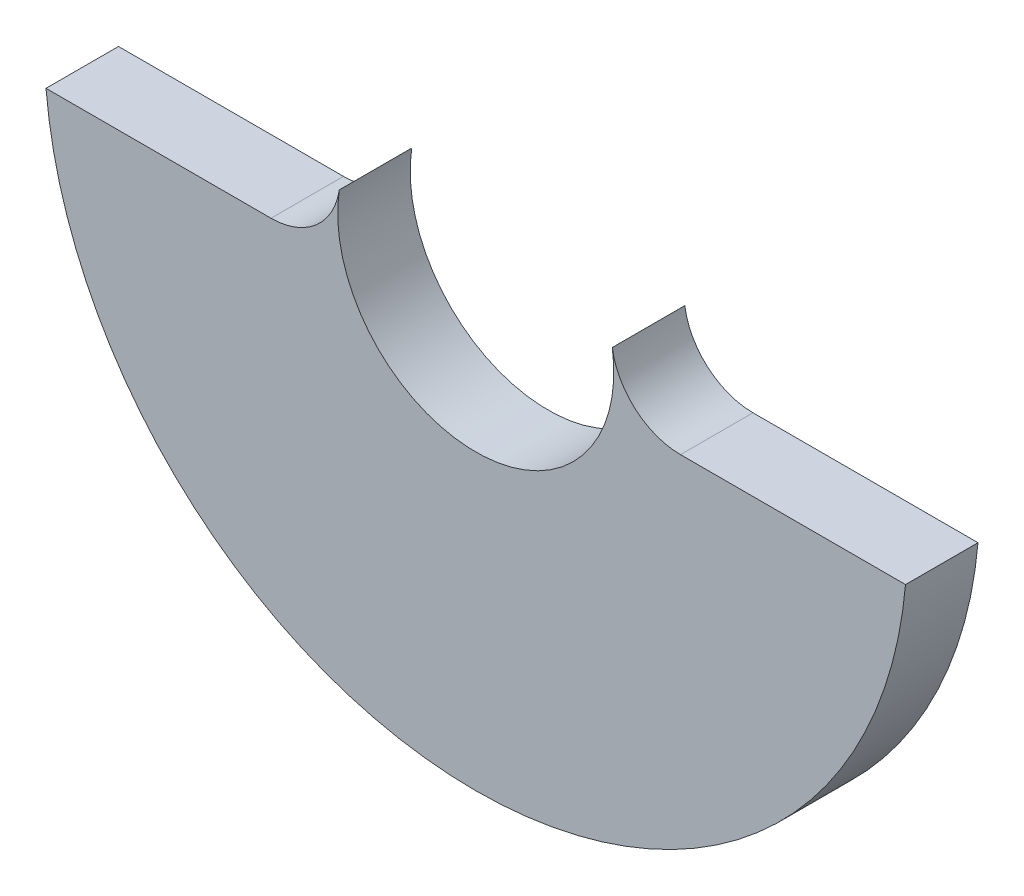
SolidWorks part; units mm, degrees
ref_plane "Front" through (0, 0, 0) normal (0, 0, 1) x (1, 0, 0)
ref_plane "Top" through (0, 0, 0) normal (0, 1, 0) x (1, 0, 0)
ref_plane "Right" through (0, 0, 0) normal (1, 0, 0) x (0, 0, -1)
sketch "Sketch1" plane through (0, 0, 0) normal (0, 0, 1) x (1, 0, 0)
  circle A0 centre (0, 0) radius 25
  circle A1 centre (0, 0) radius 8
  dimension "D1" = 50
  dimension "D2" = 16
extrude "Base-Extrude" add sketch "Sketch1" along normal blind 4.2
ref_plane "Plane1" through (0, 0, 4.2) normal (0, 0, 1) x (1, 0, 0)
sketch "Sketch2" plane through (0, 0, 4.2) normal (0, 0, 1) x (1, 0, 0)
  line L0 (-31.2832, -2.2) -> (32.4996, -2.2)
  line L1 (32.4996, -2.2) -> (32.4996, 32.6182)
  line L2 (32.4996, 32.6182) -> (-31.7393, 32.6182)
  line L3 (-31.7393, 32.6182) -> (-31.2832, -2.2)
  dimension "D1" = 2.2
extrude "Cut-Extrude1" cut sketch "Sketch2" against normal through all
ref_plane "Plane2" through (0, 0, 4.2) normal (0, 0, 1) x (1, 0, 0)
sketch "Sketch3" plane through (0, 0, 4.2) normal (0, 0, 1) x (1, 0, 0)
  line L0 (7.6916, -2.2) -> (11.8642, -2.2)
  line L1 (-11.8642, -2.2) -> (-7.6916, -2.2)
  arc A0 (-7.9095, 1.2) -> (-7.6916, -2.2) centre (0, 0) ccw
  arc A1 (-11.8642, -2.2) -> (-7.9095, 1.2) centre (-11.8642, 1.8) ccw
  arc A2 (7.9095, 1.2) -> (11.8642, -2.2) centre (11.8642, 1.8) ccw
  arc A3 (7.6916, -2.2) -> (7.9095, 1.2) centre (0, 0) ccw
  dimension "D1" = 16
  dimension "D3" = 8
  dimension "D4" = 8
  dimension "D2" = 2.2
extrude "Boss-Extrude1" add sketch "Sketch3" against normal blind 4.2
